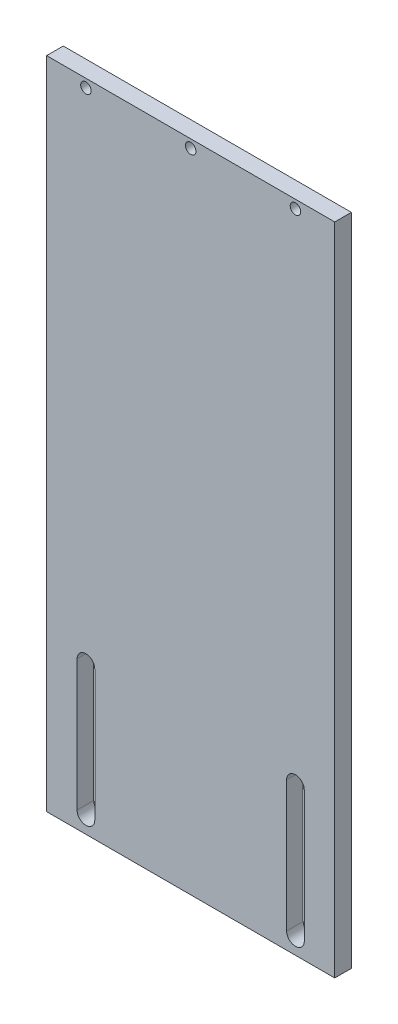
SolidWorks part; units mm, degrees
ref_plane "Alzado" through (0, 0, 0) normal (0, 0, 1) x (1, 0, 0)
ref_plane "Planta" through (0, 0, 0) normal (0, 1, 0) x (1, 0, 0)
ref_plane "Vista lateral" through (0, 0, 0) normal (1, 0, 0) x (0, 0, -1)
sketch "Croquis1" plane through (0, 0, 0) normal (0, 0, 1) x (1, 0, 0)
  line L1 (-55, -125) -> (55, -125)
  line L2 (-55, -125) -> (-55, 125)
  line L3 (-55, 125) -> (55, 125)
  line L4 (55, -125) -> (55, 125)
  line L5 (-55, -125) -> (55, 125) construction
  line L6 (-55, 125) -> (55, -125) construction
  point P0 (0, 0)
  dimension "D1" = 110
  dimension "D2" = 250
extrude "Saliente-Extruir1" add sketch "Croquis1" along normal blind 6.35
sketch "Croquis2" plane through (0, 0, 0) normal (0, 0, 1) x (1, 0, 0)
  line L0 (66.7052, 121.825) -> (-75.6472, 121.825) construction
  line L1 (55, 125) -> (-55, 125) construction
  line L2 (55, -125) -> (55, 125) construction
  line L3 (66.7052, -88.175) -> (-89.4456, -88.175) construction
  line L4 (-55, -125) -> (55, -125) construction
  line L5 (36.625, -68.65) -> (36.625, -118.65)
  line L6 (43.375, -68.65) -> (43.375, -118.65)
  line L7 (-43.375, -68.65) -> (-43.375, -118.65)
  line L8 (-36.625, -68.65) -> (-36.625, -118.65)
  circle A0 centre (40, 121.825) radius 2
  circle A1 centre (-40, 121.825) radius 2
  circle A2 centre (0, 121.825) radius 2
  arc A4 (-36.625, -68.65) -> (-43.375, -68.65) centre (-40, -68.65) ccw
  arc A5 (-43.375, -118.65) -> (-36.625, -118.65) centre (-40, -118.65) ccw
  arc A6 (43.375, -68.65) -> (36.625, -68.65) centre (40, -68.65) ccw
  arc A7 (36.625, -118.65) -> (43.375, -118.65) centre (40, -118.65) ccw
  dimension "D2" = 4
  dimension "D3" = 4
  dimension "D9" = 6.75
  dimension "D10" = 6.75
  dimension "D11" = 6.75
  dimension "D12" = 50
  dimension "D13" = 50
  dimension "D14" = 4
  dimension "D1" = 3.175
  dimension "D4" = 80
  dimension "D5" = 15
  dimension "D6" = 210
  dimension "D7" = 6.35
  dimension "D8" = 6.35
extrude "Cortar-Extruir2" cut sketch "Croquis2" along normal through all
